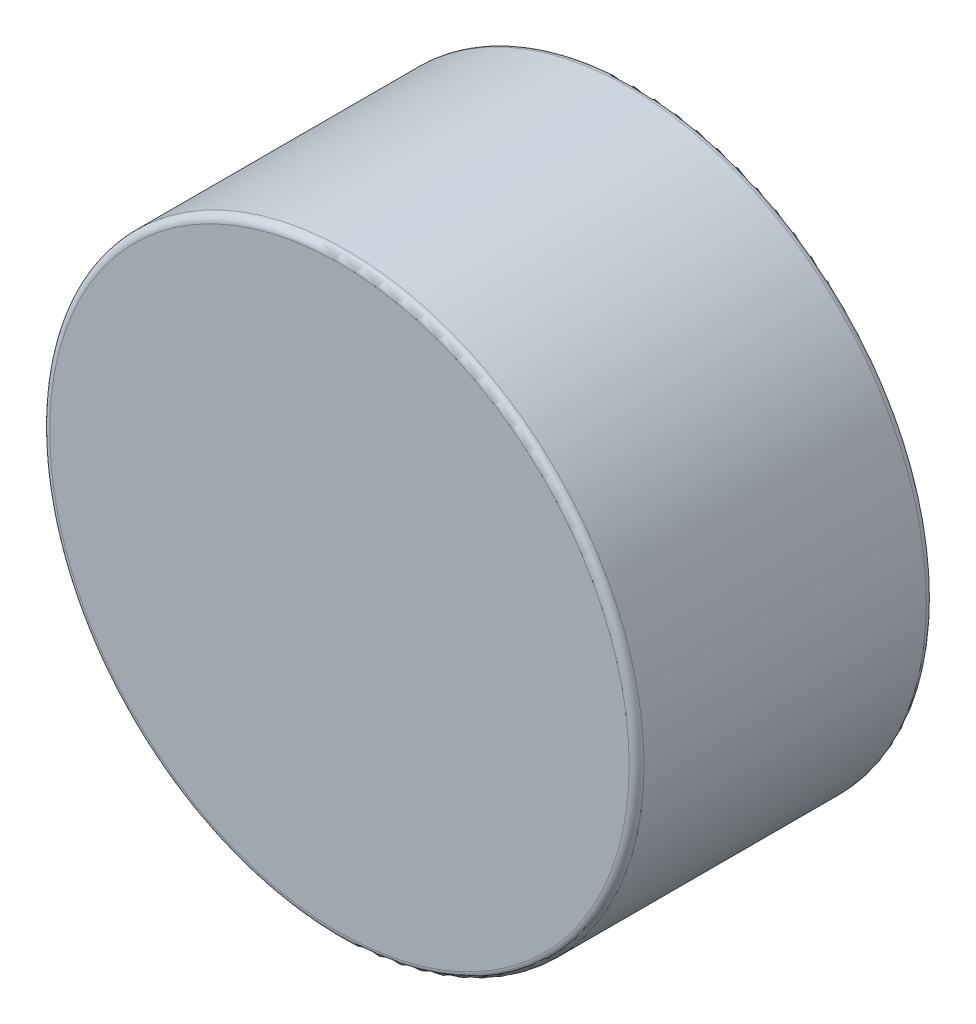
SolidWorks part; units mm, degrees
ref_plane "Front Plane" through (0, 0, 0) normal (0, 0, 1) x (1, 0, 0)
ref_plane "Top Plane" through (0, 0, 0) normal (0, 1, 0) x (1, 0, 0)
ref_plane "Right Plane" through (0, 0, 0) normal (1, 0, 0) x (0, 0, -1)
sketch "Sketch1" plane through (0, 0, 0) normal (0, 0, 1) x (1, 0, 0)
  circle A0 centre (0, 0) radius 1.5875 construction
  dimension "OD" = 3.175
sketch "Sketch2" plane through (0, 0, 0) normal (1, 0, 0) x (0, 0, -1)
  line L0 (-0.7937, 0) -> (0.7938, 0) construction
  line L1 (0, 1.5875) -> (0, -1.5875) construction
  line L3 (-0.7937, 1.5875) -> (0.7937, 1.5875)
  line L4 (-0.7937, 1.5875) -> (-0.7937, -1.5875)
  line L5 (-0.7937, -1.5875) -> (0.7938, -1.5875)
  line L6 (0.7937, 1.5875) -> (0.7938, -1.5875)
  point P4 (0, 0)
  point P12 (0, 1.5875)
  dimension "Thickness" = 1.5875
sketch "Sketch3" plane through (0, 0, 0) normal (0, 0, 1) x (1, 0, 0)
  circle A0 centre (0, 0) radius 1.5875 construction
  circle A1 centre (0, 0) radius 1.5875
extrude "Boss-Extrude1" add sketch "Sketch3" along normal up to vertex (0.7937 mm away) and the other way up to vertex (0.7937 mm away) up to point (0, 1.5875, 0.7937) other way up to point (0, 1.5875, -0.7937)
fillet "Fillet1" radius 0.0397 2 edges at (1.5875, 0, -0.7937) (1.5875, 0, 0.7937)
equation "\"Fillet@Fillet1\"=\"Thickness@Sketch2\"*.025"
